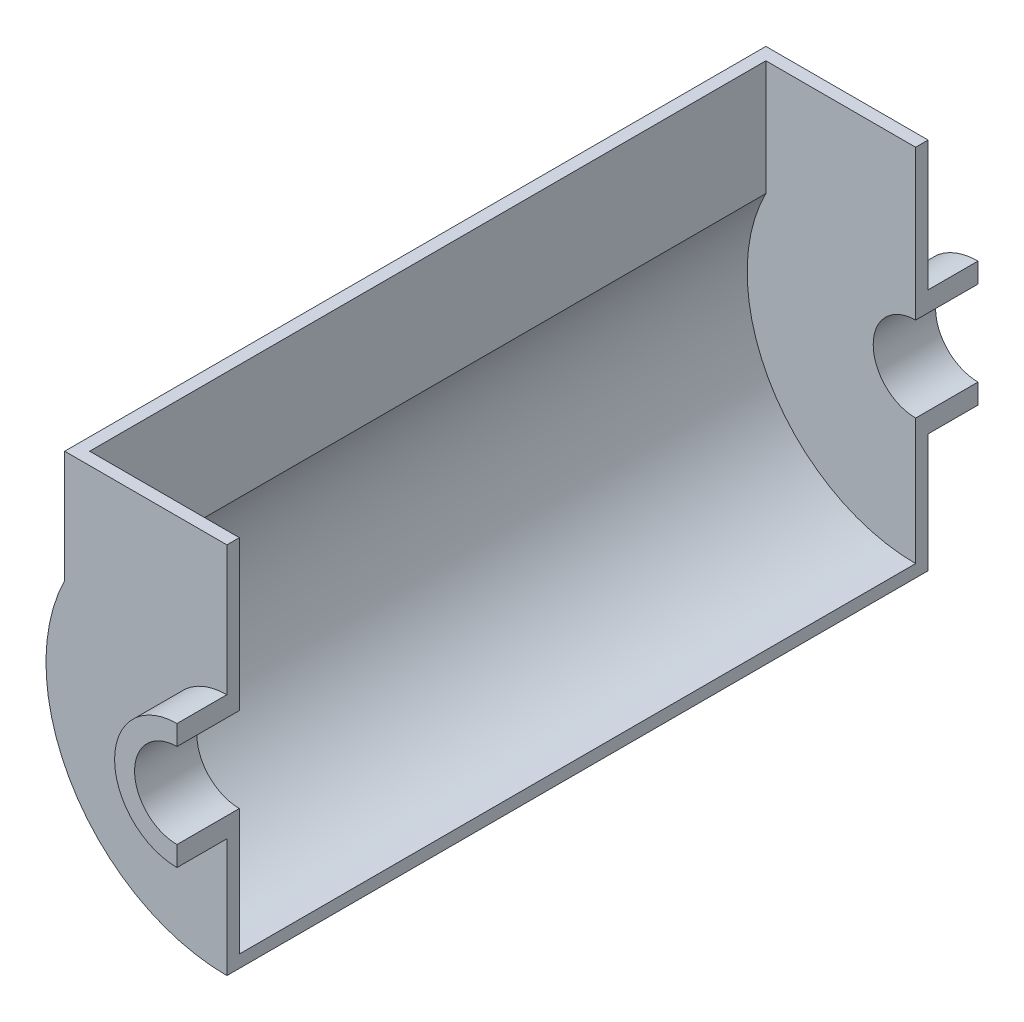
SolidWorks part; units mm, degrees
ref_plane "Front Plane" through (0, 0, 0) normal (0, 0, 1) x (1, 0, 0)
ref_plane "Top Plane" through (0, 0, 0) normal (0, 1, 0) x (1, 0, 0)
ref_plane "Right Plane" through (0, 0, 0) normal (1, 0, 0) x (0, 0, -1)
sketch "Sketch1" plane through (0, 0, 0) normal (0, 0, 1) x (1, 0, 0)
  line L0 (0, 25) -> (0, 17)
  line L1 (0, -17) -> (0, -25)
  arc A0 (0, 25) -> (0, -25) centre (0, 0) ccw
  arc A1 (0, 17) -> (0, -17) centre (0, 0) ccw
  dimension "D1" = 50
  dimension "D2" = 34
extrude "Boss-Extrude1" add sketch "Sketch1" along normal blind 20 and the other way blind 5
sketch "Sketch2" plane through (0, 0, 0) normal (0, 0, 1) x (1, 0, 0)
  line L0 (0, 25) -> (0, 77)
  line L1 (0, 77) -> (-65, 77)
  line L2 (-65, 77) -> (-65, 32.1131)
  line L3 (0, -25) -> (0, -72.5)
  line L6 (0, 17) -> (0, 25)
  line L7 (0, -25) -> (0, -17)
  arc A0 (0, -72.5) -> (-65, 32.1131) centre (0, 0) cw
  arc A3 (0, 17) -> (0, -17) centre (0, 0) ccw
  arc A4 (0, 25) -> (0, -25) centre (0, 0) ccw
  arc A6 (0, 25) -> (0, -25) centre (0, 0) ccw
  point P10 (0, 0)
  dimension "D3" = 72.5
  dimension "D1" = 52
  dimension "D2" = 65
  dimension "D4" = 0
extrude "Boss-Extrude2" add sketch "Sketch2" against normal blind 5
ref_plane "Plane1" through (0, 0, -140.5) normal (0, 0, 1) x (1, 0, 0)
mirror "Mirror2" about plane through (0, 0, -140.5) normal (0, 0, 1) of bodies 102
sketch "Sketch3" plane through (0, 0, -5) normal (0, 0, -1) x (-1, 0, 0)
  line L0 (60, 30.9233) -> (60, 77)
  line L1 (0, -72.5) -> (0, -67.5)
  line L2 (65, 77) -> (60, 77)
  line L4 (0, -17) -> (0, -72.5)
  line L5 (65, 32.1131) -> (65, 77)
  line L6 (65, 77) -> (0, 77)
  line L7 (0, 77) -> (0, 17)
  line L8 (0, -17) -> (0, -72.5)
  line L9 (65, 32.1131) -> (65, 77)
  line L10 (65, 77) -> (0, 77)
  line L11 (0, 77) -> (0, 17)
  arc A0 (0, -67.5) -> (60, 30.9233) centre (0, 0) ccw
  arc A2 (0, -17) -> (0, 17) centre (0, 0) ccw
  arc A3 (0, -72.5) -> (65, 32.1131) centre (0, 0) ccw
  arc A4 (0, -17) -> (0, 17) centre (0, 0) ccw
  arc A5 (0, -72.5) -> (65, 32.1131) centre (0, 0) ccw
  line M8 (0, -17) -> (0, -72.5)
  arc M9 (0, -72.5) -> (65, 32.1131) centre (0, 0) ccw
  line M10 (65, 32.1131) -> (65, 77)
  line M11 (65, 77) -> (0, 77)
  dimension "D1" = 0
  dimension "D2" = 5
extrude "Boss-Extrude3" add sketch "Sketch3" along normal up to surface (271 mm away) contours A0 L0 M8 M9 M10 M11
